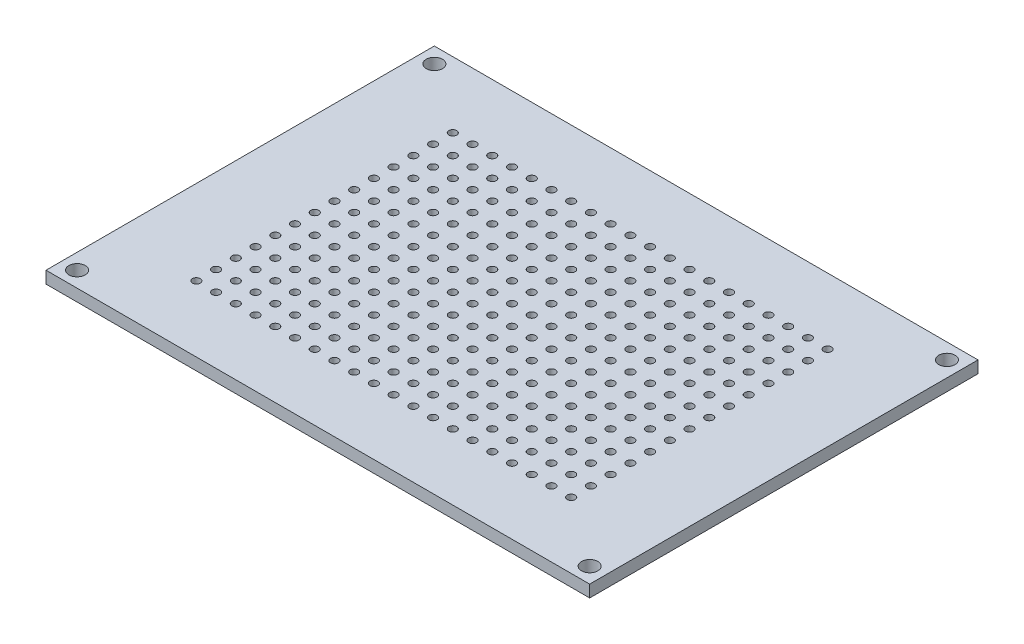
SolidWorks part; units mm, degrees
ref_plane "Front Plane" through (0, 0, 0) normal (0, 0, 1) x (1, 0, 0)
ref_plane "Top Plane" through (0, 0, 0) normal (0, 1, 0) x (1, 0, 0)
ref_plane "Right Plane" through (0, 0, 0) normal (1, 0, 0) x (0, 0, -1)
sketch "Sketch1" plane through (0, 0, 0) normal (0, 1, 0) x (1, 0, 0)
  line L0 (0, 50) -> (70, 0) construction
  line L1 (0, 0) -> (70, 0)
  line L2 (0, 0) -> (0, 50)
  line L3 (0, 50) -> (70, 50)
  line L4 (70, 0) -> (70, 50)
  line L5 (0, 0) -> (70, 50) construction
  line L6 (35, 25) -> (35, 1.3853) construction
  line L7 (35, 25) -> (7.4762, 25) construction
  circle A0 centre (33.73, 23.73) radius 0.508
  circle A1 centre (36.27, 23.73) radius 0.508
  circle A2 centre (38.81, 23.73) radius 0.508
  circle A3 centre (41.35, 23.73) radius 0.508
  circle A4 centre (43.89, 23.73) radius 0.508
  circle A5 centre (46.43, 23.73) radius 0.508
  circle A6 centre (48.97, 23.73) radius 0.508
  circle A7 centre (51.51, 23.73) radius 0.508
  circle A8 centre (54.05, 23.73) radius 0.508
  circle A9 centre (56.59, 23.73) radius 0.508
  circle A10 centre (59.13, 23.73) radius 0.508
  circle A11 centre (36.27, 26.27) radius 0.508
  circle A12 centre (38.81, 26.27) radius 0.508
  circle A13 centre (41.35, 26.27) radius 0.508
  circle A14 centre (43.89, 26.27) radius 0.508
  circle A15 centre (46.43, 26.27) radius 0.508
  circle A16 centre (48.97, 26.27) radius 0.508
  circle A17 centre (51.51, 26.27) radius 0.508
  circle A18 centre (54.05, 26.27) radius 0.508
  circle A19 centre (56.59, 26.27) radius 0.508
  circle A20 centre (59.13, 26.27) radius 0.508
  circle A21 centre (36.27, 28.81) radius 0.508
  circle A22 centre (38.81, 28.81) radius 0.508
  circle A23 centre (41.35, 28.81) radius 0.508
  circle A24 centre (43.89, 28.81) radius 0.508
  circle A25 centre (46.43, 28.81) radius 0.508
  circle A26 centre (48.97, 28.81) radius 0.508
  circle A27 centre (51.51, 28.81) radius 0.508
  circle A28 centre (54.05, 28.81) radius 0.508
  circle A29 centre (56.59, 28.81) radius 0.508
  circle A30 centre (59.13, 28.81) radius 0.508
  circle A31 centre (36.27, 31.35) radius 0.508
  circle A32 centre (38.81, 31.35) radius 0.508
  circle A33 centre (41.35, 31.35) radius 0.508
  circle A34 centre (43.89, 31.35) radius 0.508
  circle A35 centre (46.43, 31.35) radius 0.508
  circle A36 centre (48.97, 31.35) radius 0.508
  circle A37 centre (51.51, 31.35) radius 0.508
  circle A38 centre (54.05, 31.35) radius 0.508
  circle A39 centre (56.59, 31.35) radius 0.508
  circle A40 centre (59.13, 31.35) radius 0.508
  circle A41 centre (36.27, 33.89) radius 0.508
  circle A42 centre (38.81, 33.89) radius 0.508
  circle A43 centre (41.35, 33.89) radius 0.508
  circle A44 centre (43.89, 33.89) radius 0.508
  circle A45 centre (46.43, 33.89) radius 0.508
  circle A46 centre (48.97, 33.89) radius 0.508
  circle A47 centre (51.51, 33.89) radius 0.508
  circle A48 centre (54.05, 33.89) radius 0.508
  circle A49 centre (56.59, 33.89) radius 0.508
  circle A50 centre (59.13, 33.89) radius 0.508
  circle A51 centre (36.27, 36.43) radius 0.508
  circle A52 centre (38.81, 36.43) radius 0.508
  circle A53 centre (41.35, 36.43) radius 0.508
  circle A54 centre (43.89, 36.43) radius 0.508
  circle A55 centre (46.43, 36.43) radius 0.508
  circle A56 centre (48.97, 36.43) radius 0.508
  circle A57 centre (51.51, 36.43) radius 0.508
  circle A58 centre (54.05, 36.43) radius 0.508
  circle A59 centre (56.59, 36.43) radius 0.508
  circle A60 centre (59.13, 36.43) radius 0.508
  circle A61 centre (36.27, 38.97) radius 0.508
  circle A62 centre (38.81, 38.97) radius 0.508
  circle A63 centre (41.35, 38.97) radius 0.508
  circle A64 centre (43.89, 38.97) radius 0.508
  circle A65 centre (46.43, 38.97) radius 0.508
  circle A66 centre (48.97, 38.97) radius 0.508
  circle A67 centre (51.51, 38.97) radius 0.508
  circle A68 centre (54.05, 38.97) radius 0.508
  circle A69 centre (56.59, 38.97) radius 0.508
  circle A70 centre (59.13, 38.97) radius 0.508
  circle A71 centre (36.27, 41.51) radius 0.508
  circle A72 centre (38.81, 41.51) radius 0.508
  circle A73 centre (41.35, 41.51) radius 0.508
  circle A74 centre (43.89, 41.51) radius 0.508
  circle A75 centre (46.43, 41.51) radius 0.508
  circle A76 centre (48.97, 41.51) radius 0.508
  circle A77 centre (51.51, 41.51) radius 0.508
  circle A78 centre (54.05, 41.51) radius 0.508
  circle A79 centre (56.59, 41.51) radius 0.508
  circle A80 centre (59.13, 41.51) radius 0.508
  circle A81 centre (33.73, 26.27) radius 0.508
  circle A82 centre (33.73, 28.81) radius 0.508
  circle A83 centre (33.73, 31.35) radius 0.508
  circle A84 centre (33.73, 33.89) radius 0.508
  circle A85 centre (33.73, 36.43) radius 0.508
  circle A86 centre (33.73, 38.97) radius 0.508
  circle A87 centre (33.73, 41.51) radius 0.508
  circle A88 centre (56.59, 41.51) radius 0.508
  circle A89 centre (54.05, 41.51) radius 0.508
  circle A90 centre (51.51, 41.51) radius 0.508
  circle A91 centre (48.97, 41.51) radius 0.508
  circle A92 centre (46.43, 41.51) radius 0.508
  circle A93 centre (43.89, 41.51) radius 0.508
  circle A94 centre (41.35, 41.51) radius 0.508
  circle A95 centre (38.81, 41.51) radius 0.508
  circle A96 centre (36.27, 41.51) radius 0.508
  circle A97 centre (33.73, 41.51) radius 0.508
  circle A98 centre (31.19, 41.51) radius 0.508
  circle A99 centre (28.65, 41.51) radius 0.508
  circle A100 centre (26.11, 41.51) radius 0.508
  circle A101 centre (23.57, 41.51) radius 0.508
  circle A102 centre (21.03, 41.51) radius 0.508
  circle A103 centre (18.49, 41.51) radius 0.508
  circle A104 centre (15.95, 41.51) radius 0.508
  circle A105 centre (13.41, 41.51) radius 0.508
  circle A106 centre (10.87, 41.51) radius 0.508
  circle A107 centre (56.59, 38.97) radius 0.508
  circle A108 centre (54.05, 38.97) radius 0.508
  circle A109 centre (51.51, 38.97) radius 0.508
  circle A110 centre (48.97, 38.97) radius 0.508
  circle A111 centre (46.43, 38.97) radius 0.508
  circle A112 centre (43.89, 38.97) radius 0.508
  circle A113 centre (41.35, 38.97) radius 0.508
  circle A114 centre (38.81, 38.97) radius 0.508
  circle A115 centre (36.27, 38.97) radius 0.508
  circle A116 centre (33.73, 38.97) radius 0.508
  circle A117 centre (31.19, 38.97) radius 0.508
  circle A118 centre (28.65, 38.97) radius 0.508
  circle A119 centre (26.11, 38.97) radius 0.508
  circle A120 centre (23.57, 38.97) radius 0.508
  circle A121 centre (21.03, 38.97) radius 0.508
  circle A122 centre (18.49, 38.97) radius 0.508
  circle A123 centre (15.95, 38.97) radius 0.508
  circle A124 centre (13.41, 38.97) radius 0.508
  circle A125 centre (10.87, 38.97) radius 0.508
  circle A126 centre (56.59, 36.43) radius 0.508
  circle A127 centre (54.05, 36.43) radius 0.508
  circle A128 centre (51.51, 36.43) radius 0.508
  circle A129 centre (48.97, 36.43) radius 0.508
  circle A130 centre (46.43, 36.43) radius 0.508
  circle A131 centre (43.89, 36.43) radius 0.508
  circle A132 centre (41.35, 36.43) radius 0.508
  circle A133 centre (38.81, 36.43) radius 0.508
  circle A134 centre (36.27, 36.43) radius 0.508
  circle A135 centre (33.73, 36.43) radius 0.508
  circle A136 centre (31.19, 36.43) radius 0.508
  circle A137 centre (28.65, 36.43) radius 0.508
  circle A138 centre (26.11, 36.43) radius 0.508
  circle A139 centre (23.57, 36.43) radius 0.508
  circle A140 centre (21.03, 36.43) radius 0.508
  circle A141 centre (18.49, 36.43) radius 0.508
  circle A142 centre (15.95, 36.43) radius 0.508
  circle A143 centre (13.41, 36.43) radius 0.508
  circle A144 centre (10.87, 36.43) radius 0.508
  circle A145 centre (56.59, 33.89) radius 0.508
  circle A146 centre (54.05, 33.89) radius 0.508
  circle A147 centre (51.51, 33.89) radius 0.508
  circle A148 centre (48.97, 33.89) radius 0.508
  circle A149 centre (46.43, 33.89) radius 0.508
  circle A150 centre (43.89, 33.89) radius 0.508
  circle A151 centre (41.35, 33.89) radius 0.508
  circle A152 centre (38.81, 33.89) radius 0.508
  circle A153 centre (36.27, 33.89) radius 0.508
  circle A154 centre (33.73, 33.89) radius 0.508
  circle A155 centre (31.19, 33.89) radius 0.508
  circle A156 centre (28.65, 33.89) radius 0.508
  circle A157 centre (26.11, 33.89) radius 0.508
  circle A158 centre (23.57, 33.89) radius 0.508
  circle A159 centre (21.03, 33.89) radius 0.508
  circle A160 centre (18.49, 33.89) radius 0.508
  circle A161 centre (15.95, 33.89) radius 0.508
  circle A162 centre (13.41, 33.89) radius 0.508
  circle A163 centre (10.87, 33.89) radius 0.508
  circle A164 centre (56.59, 31.35) radius 0.508
  circle A165 centre (54.05, 31.35) radius 0.508
  circle A166 centre (51.51, 31.35) radius 0.508
  circle A167 centre (48.97, 31.35) radius 0.508
  circle A168 centre (46.43, 31.35) radius 0.508
  circle A169 centre (43.89, 31.35) radius 0.508
  circle A170 centre (41.35, 31.35) radius 0.508
  circle A171 centre (38.81, 31.35) radius 0.508
  circle A172 centre (36.27, 31.35) radius 0.508
  circle A173 centre (33.73, 31.35) radius 0.508
  circle A174 centre (31.19, 31.35) radius 0.508
  circle A175 centre (28.65, 31.35) radius 0.508
  circle A176 centre (26.11, 31.35) radius 0.508
  circle A177 centre (23.57, 31.35) radius 0.508
  circle A178 centre (21.03, 31.35) radius 0.508
  circle A179 centre (18.49, 31.35) radius 0.508
  circle A180 centre (15.95, 31.35) radius 0.508
  circle A181 centre (13.41, 31.35) radius 0.508
  circle A182 centre (10.87, 31.35) radius 0.508
  circle A183 centre (56.59, 28.81) radius 0.508
  circle A184 centre (54.05, 28.81) radius 0.508
  circle A185 centre (51.51, 28.81) radius 0.508
  circle A186 centre (48.97, 28.81) radius 0.508
  circle A187 centre (46.43, 28.81) radius 0.508
  circle A188 centre (43.89, 28.81) radius 0.508
  circle A189 centre (41.35, 28.81) radius 0.508
  circle A190 centre (38.81, 28.81) radius 0.508
  circle A191 centre (36.27, 28.81) radius 0.508
  circle A192 centre (33.73, 28.81) radius 0.508
  circle A193 centre (31.19, 28.81) radius 0.508
  circle A194 centre (28.65, 28.81) radius 0.508
  circle A195 centre (26.11, 28.81) radius 0.508
  circle A196 centre (23.57, 28.81) radius 0.508
  circle A197 centre (21.03, 28.81) radius 0.508
  circle A198 centre (18.49, 28.81) radius 0.508
  circle A199 centre (15.95, 28.81) radius 0.508
  circle A200 centre (13.41, 28.81) radius 0.508
  circle A201 centre (10.87, 28.81) radius 0.508
  circle A202 centre (56.59, 26.27) radius 0.508
  circle A203 centre (54.05, 26.27) radius 0.508
  circle A204 centre (51.51, 26.27) radius 0.508
  circle A205 centre (48.97, 26.27) radius 0.508
  circle A206 centre (46.43, 26.27) radius 0.508
  circle A207 centre (43.89, 26.27) radius 0.508
  circle A208 centre (41.35, 26.27) radius 0.508
  circle A209 centre (38.81, 26.27) radius 0.508
  circle A210 centre (36.27, 26.27) radius 0.508
  circle A211 centre (33.73, 26.27) radius 0.508
  circle A212 centre (31.19, 26.27) radius 0.508
  circle A213 centre (28.65, 26.27) radius 0.508
  circle A214 centre (26.11, 26.27) radius 0.508
  circle A215 centre (23.57, 26.27) radius 0.508
  circle A216 centre (21.03, 26.27) radius 0.508
  circle A217 centre (18.49, 26.27) radius 0.508
  circle A218 centre (15.95, 26.27) radius 0.508
  circle A219 centre (13.41, 26.27) radius 0.508
  circle A220 centre (10.87, 26.27) radius 0.508
  circle A221 centre (56.59, 23.73) radius 0.508
  circle A222 centre (54.05, 23.73) radius 0.508
  circle A223 centre (51.51, 23.73) radius 0.508
  circle A224 centre (48.97, 23.73) radius 0.508
  circle A225 centre (46.43, 23.73) radius 0.508
  circle A226 centre (43.89, 23.73) radius 0.508
  circle A227 centre (41.35, 23.73) radius 0.508
  circle A228 centre (38.81, 23.73) radius 0.508
  circle A229 centre (36.27, 23.73) radius 0.508
  circle A230 centre (33.73, 23.73) radius 0.508
  circle A231 centre (31.19, 23.73) radius 0.508
  circle A232 centre (28.65, 23.73) radius 0.508
  circle A233 centre (26.11, 23.73) radius 0.508
  circle A234 centre (23.57, 23.73) radius 0.508
  circle A235 centre (21.03, 23.73) radius 0.508
  circle A236 centre (18.49, 23.73) radius 0.508
  circle A237 centre (15.95, 23.73) radius 0.508
  circle A238 centre (13.41, 23.73) radius 0.508
  circle A239 centre (10.87, 23.73) radius 0.508
  circle A240 centre (56.59, 21.19) radius 0.508
  circle A241 centre (54.05, 21.19) radius 0.508
  circle A242 centre (51.51, 21.19) radius 0.508
  circle A243 centre (48.97, 21.19) radius 0.508
  circle A244 centre (46.43, 21.19) radius 0.508
  circle A245 centre (43.89, 21.19) radius 0.508
  circle A246 centre (41.35, 21.19) radius 0.508
  circle A247 centre (38.81, 21.19) radius 0.508
  circle A248 centre (36.27, 21.19) radius 0.508
  circle A249 centre (33.73, 21.19) radius 0.508
  circle A250 centre (31.19, 21.19) radius 0.508
  circle A251 centre (28.65, 21.19) radius 0.508
  circle A252 centre (26.11, 21.19) radius 0.508
  circle A253 centre (23.57, 21.19) radius 0.508
  circle A254 centre (21.03, 21.19) radius 0.508
  circle A255 centre (18.49, 21.19) radius 0.508
  circle A256 centre (15.95, 21.19) radius 0.508
  circle A257 centre (13.41, 21.19) radius 0.508
  circle A258 centre (10.87, 21.19) radius 0.508
  circle A259 centre (56.59, 18.65) radius 0.508
  circle A260 centre (54.05, 18.65) radius 0.508
  circle A261 centre (51.51, 18.65) radius 0.508
  circle A262 centre (48.97, 18.65) radius 0.508
  circle A263 centre (46.43, 18.65) radius 0.508
  circle A264 centre (43.89, 18.65) radius 0.508
  circle A265 centre (41.35, 18.65) radius 0.508
  circle A266 centre (38.81, 18.65) radius 0.508
  circle A267 centre (36.27, 18.65) radius 0.508
  circle A268 centre (33.73, 18.65) radius 0.508
  circle A269 centre (31.19, 18.65) radius 0.508
  circle A270 centre (28.65, 18.65) radius 0.508
  circle A271 centre (26.11, 18.65) radius 0.508
  circle A272 centre (23.57, 18.65) radius 0.508
  circle A273 centre (21.03, 18.65) radius 0.508
  circle A274 centre (18.49, 18.65) radius 0.508
  circle A275 centre (15.95, 18.65) radius 0.508
  circle A276 centre (13.41, 18.65) radius 0.508
  circle A277 centre (10.87, 18.65) radius 0.508
  circle A278 centre (56.59, 16.11) radius 0.508
  circle A279 centre (54.05, 16.11) radius 0.508
  circle A280 centre (51.51, 16.11) radius 0.508
  circle A281 centre (48.97, 16.11) radius 0.508
  circle A282 centre (46.43, 16.11) radius 0.508
  circle A283 centre (43.89, 16.11) radius 0.508
  circle A284 centre (41.35, 16.11) radius 0.508
  circle A285 centre (38.81, 16.11) radius 0.508
  circle A286 centre (36.27, 16.11) radius 0.508
  circle A287 centre (33.73, 16.11) radius 0.508
  circle A288 centre (31.19, 16.11) radius 0.508
  circle A289 centre (28.65, 16.11) radius 0.508
  circle A290 centre (26.11, 16.11) radius 0.508
  circle A291 centre (23.57, 16.11) radius 0.508
  circle A292 centre (21.03, 16.11) radius 0.508
  circle A293 centre (18.49, 16.11) radius 0.508
  circle A294 centre (15.95, 16.11) radius 0.508
  circle A295 centre (13.41, 16.11) radius 0.508
  circle A296 centre (10.87, 16.11) radius 0.508
  circle A297 centre (56.59, 13.57) radius 0.508
  circle A298 centre (54.05, 13.57) radius 0.508
  circle A299 centre (51.51, 13.57) radius 0.508
  circle A300 centre (48.97, 13.57) radius 0.508
  circle A301 centre (46.43, 13.57) radius 0.508
  circle A302 centre (43.89, 13.57) radius 0.508
  circle A303 centre (41.35, 13.57) radius 0.508
  circle A304 centre (38.81, 13.57) radius 0.508
  circle A305 centre (36.27, 13.57) radius 0.508
  circle A306 centre (33.73, 13.57) radius 0.508
  circle A307 centre (31.19, 13.57) radius 0.508
  circle A308 centre (28.65, 13.57) radius 0.508
  circle A309 centre (26.11, 13.57) radius 0.508
  circle A310 centre (23.57, 13.57) radius 0.508
  circle A311 centre (21.03, 13.57) radius 0.508
  circle A312 centre (18.49, 13.57) radius 0.508
  circle A313 centre (15.95, 13.57) radius 0.508
  circle A314 centre (13.41, 13.57) radius 0.508
  circle A315 centre (10.87, 13.57) radius 0.508
  circle A316 centre (56.59, 11.03) radius 0.508
  circle A317 centre (54.05, 11.03) radius 0.508
  circle A318 centre (51.51, 11.03) radius 0.508
  circle A319 centre (48.97, 11.03) radius 0.508
  circle A320 centre (46.43, 11.03) radius 0.508
  circle A321 centre (43.89, 11.03) radius 0.508
  circle A322 centre (41.35, 11.03) radius 0.508
  circle A323 centre (38.81, 11.03) radius 0.508
  circle A324 centre (36.27, 11.03) radius 0.508
  circle A325 centre (33.73, 11.03) radius 0.508
  circle A326 centre (31.19, 11.03) radius 0.508
  circle A327 centre (28.65, 11.03) radius 0.508
  circle A328 centre (26.11, 11.03) radius 0.508
  circle A329 centre (23.57, 11.03) radius 0.508
  circle A330 centre (21.03, 11.03) radius 0.508
  circle A331 centre (18.49, 11.03) radius 0.508
  circle A332 centre (15.95, 11.03) radius 0.508
  circle A333 centre (13.41, 11.03) radius 0.508
  circle A334 centre (10.87, 11.03) radius 0.508
  circle A335 centre (56.59, 8.49) radius 0.508
  circle A336 centre (54.05, 8.49) radius 0.508
  circle A337 centre (51.51, 8.49) radius 0.508
  circle A338 centre (48.97, 8.49) radius 0.508
  circle A339 centre (46.43, 8.49) radius 0.508
  circle A340 centre (43.89, 8.49) radius 0.508
  circle A341 centre (41.35, 8.49) radius 0.508
  circle A342 centre (38.81, 8.49) radius 0.508
  circle A343 centre (36.27, 8.49) radius 0.508
  circle A344 centre (33.73, 8.49) radius 0.508
  circle A345 centre (31.19, 8.49) radius 0.508
  circle A346 centre (28.65, 8.49) radius 0.508
  circle A347 centre (26.11, 8.49) radius 0.508
  circle A348 centre (23.57, 8.49) radius 0.508
  circle A349 centre (21.03, 8.49) radius 0.508
  circle A350 centre (18.49, 8.49) radius 0.508
  circle A351 centre (15.95, 8.49) radius 0.508
  circle A352 centre (13.41, 8.49) radius 0.508
  circle A353 centre (10.87, 8.49) radius 0.508
  circle A354 centre (59.13, 38.97) radius 0.508
  circle A355 centre (59.13, 36.43) radius 0.508
  circle A356 centre (59.13, 33.89) radius 0.508
  circle A357 centre (59.13, 31.35) radius 0.508
  circle A358 centre (59.13, 28.81) radius 0.508
  circle A359 centre (59.13, 26.27) radius 0.508
  circle A360 centre (59.13, 23.73) radius 0.508
  circle A361 centre (59.13, 21.19) radius 0.508
  circle A362 centre (59.13, 18.65) radius 0.508
  circle A363 centre (59.13, 16.11) radius 0.508
  circle A364 centre (59.13, 13.57) radius 0.508
  circle A365 centre (59.13, 11.03) radius 0.508
  circle A366 centre (59.13, 8.49) radius 0.508
  circle A367 centre (2, 2) radius 1.05
  circle A368 centre (68, 2) radius 1.05
  circle A369 centre (68, 48) radius 1.05
  circle A370 centre (2, 48) radius 1.05
  point P7 (35, 25)
  dimension "D4" = 1.016
  dimension "D12" = 2.1
  dimension "D1" = 70
  dimension "D2" = 50
  dimension "D3" = 1.27
  dimension "D5" = 1.27
  dimension "D10" = 2
  dimension "D11" = 2
  dimension "D6" = 11
  dimension "D7" = 8
  dimension "D8" = 20
  dimension "D9" = 14
extrude "Boss-Extrude1" add sketch "Sketch1" along normal blind 1.55
ref_plane "Plane1" through (30, 0, 0) normal (1, 0, 0) x (0, 0, -1)
ref_plane "Plane2" through (0, 0, -20) normal (0, 0, 1) x (1, 0, 0)
ref_plane "Plane3" through (0, 0, -25) normal (0, 0, 1) x (1, 0, 0)
